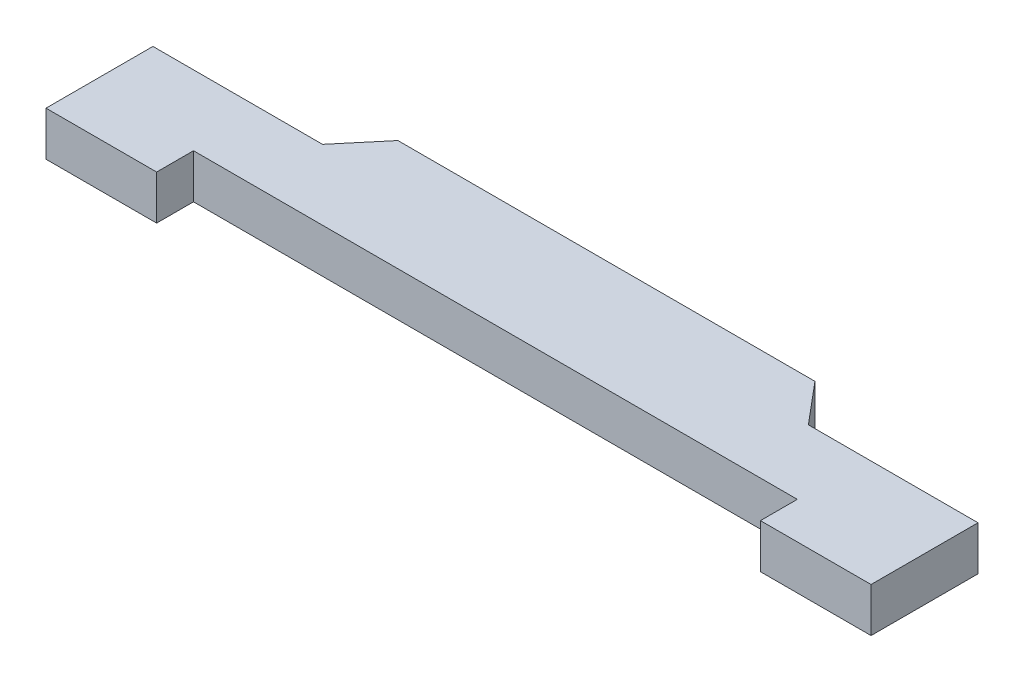
SolidWorks part; units mm, degrees
ref_plane "Front" through (0, 0, 0) normal (0, 0, 1) x (1, 0, 0)
ref_plane "Top" through (0, 0, 0) normal (0, 1, 0) x (1, 0, 0)
ref_plane "Right" through (0, 0, 0) normal (1, 0, 0) x (0, 0, -1)
sketch "Sketch1" plane through (0, 0, 0) normal (0, 1, 0) x (1, 0, 0)
  line L0 (5.655, 3.0108) -> (-5.655, 3.0108)
  line L1 (-5.655, 3.0108) -> (-6.587, 1.9)
  line L2 (-6.587, 1.9) -> (-11.187, 1.9)
  line L3 (-11.187, 1.9) -> (-11.187, -1)
  line L4 (-11.187, -1) -> (-8.187, -1)
  line L5 (-8.187, -1) -> (-8.187, 0)
  line L6 (-8.187, 0) -> (8.187, 0)
  line L7 (0, 0) -> (0, -50000) construction
  line L8 (8.187, -1) -> (8.187, 0)
  line L9 (11.187, -1) -> (8.187, -1)
  line L10 (11.187, 1.9) -> (11.187, -1)
  line L11 (6.587, 1.9) -> (11.187, 1.9)
  line L12 (5.655, 3.0108) -> (6.587, 1.9)
  point P12 (0, 0)
  point P17 (0, 3.0108)
  dimension "D1" = 5.655
  dimension "D2" = 230
  dimension "D3" = 1.45
  dimension "D4" = 4.6
  dimension "D5" = 2.9
  dimension "D6" = 3
  dimension "D7" = 1
extrude "Boss-Extrude1" add sketch "Sketch1" along normal blind 1.2
